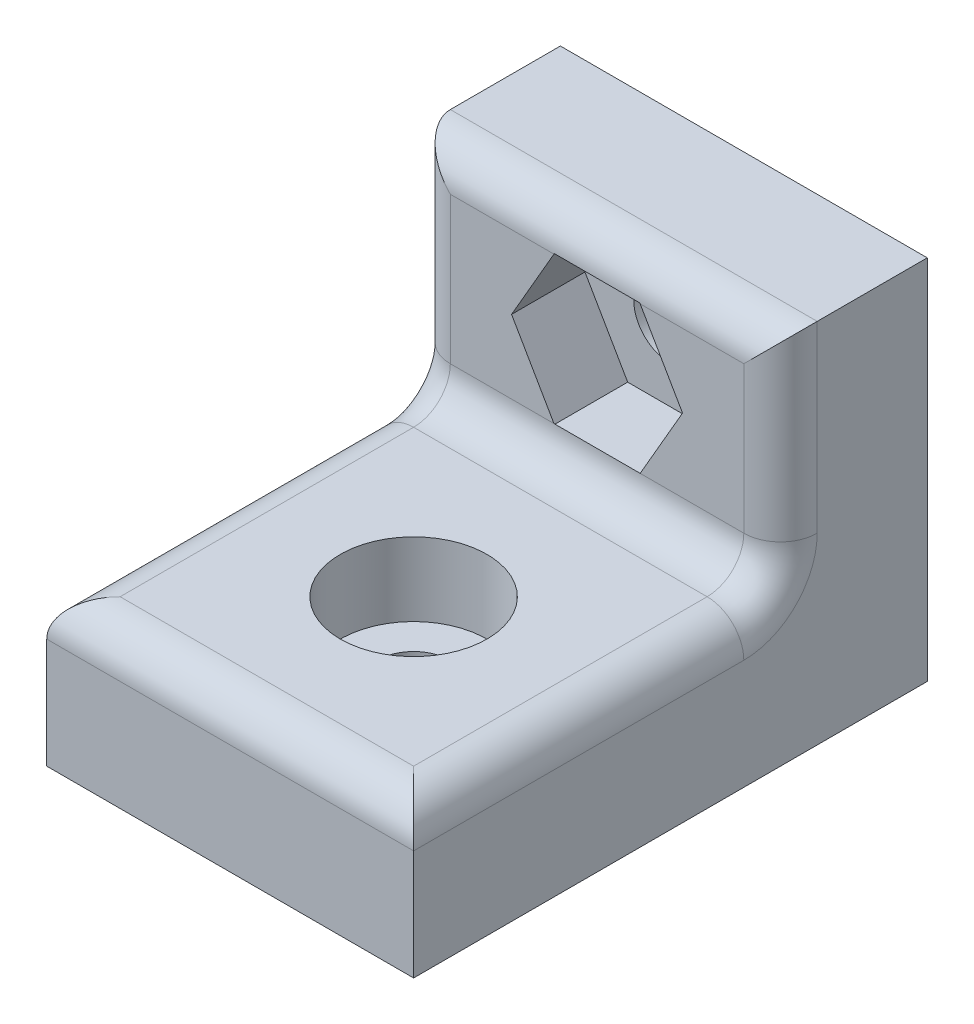
SolidWorks part; units mm, degrees
ref_plane "Plan de face" through (0, 0, 0) normal (0, 0, 1) x (1, 0, 0)
ref_plane "Plan de dessus" through (0, 0, 0) normal (0, 1, 0) x (1, 0, 0)
ref_plane "Plan de droite" through (0, 0, 0) normal (1, 0, 0) x (0, 0, -1)
sketch "Esquisse1" plane through (0, 0, 0) normal (0, 0, 1) x (1, 0, 0)
  line L1 (-5, 10) -> (5, 10)
  line L2 (-5, 10) -> (-5, 0)
  line L3 (-5, 0) -> (5, 0)
  line L4 (5, 10) -> (5, 0)
  dimension "D1" = 10
  dimension "D2" = 10
  dimension "D3" = 5
extrude "Boss.-Extru.1" add sketch "Esquisse1" along normal blind 4
sketch "Esquisse2" plane through (0, 0, 4) normal (0, 0, 1) x (1, 0, 0)
  line L0 (5, 0) -> (5, 10) construction
  line L1 (-5, 0) -> (5, 0)
  line L2 (-5, 0) -> (-5, 4)
  line L3 (-5, 4) -> (5, 4)
  line L4 (5, 0) -> (5, 4)
  dimension "D1" = 4
extrude "Boss.-Extru.2" add sketch "Esquisse2" along normal blind 10
sketch "Esquisse3" plane through (0, 0, 4) normal (0, 0, 1) x (1, 0, 0)
  line L0 (5, 10) -> (-5, 10) construction
  line L1 (-5, 10) -> (-5, 4) construction
  circle A0 centre (0, 7) radius 1
  point P2 (0, 10)
  point P3 (-5, 7)
  dimension "D1" = 2
extrude "Enlèv. mat.-Extru.1" cut sketch "Esquisse3" against normal through all
fillet "Congé1" radius 1 7 edges at (0, 4, 4) (5, 7, 4) (-5, 7, 4) (0, 10, 4) (0, 4, 14) (5, 4, 9) (-5, 4, 9)
sketch "Esquisse4" plane through (0, 4, 0) normal (0, 1, 0) x (1, 0, 0)
  line L0 (5, -14) -> (-5, -14) construction
  line L1 (-5, -14) -> (-5, -4) construction
  circle A0 centre (0, -9) radius 1
  point P0 (0, -14)
  point P1 (-5, -9)
  dimension "D1" = 2
extrude "Enlèv. mat.-Extru.2" cut sketch "Esquisse4" against normal through all
sketch "Esquisse5" plane through (0, 0, 4) normal (0, 0, 1) x (1, 0, 0)
  line L0 (5, 10) -> (-5, 10) construction
  line L1 (1.165, 4.9822) -> (2.33, 7)
  line L2 (2.33, 7) -> (1.165, 9.0178)
  line L3 (1.165, 9.0178) -> (-1.165, 9.0178)
  line L4 (-1.165, 9.0178) -> (-2.33, 7)
  line L5 (-2.33, 7) -> (-1.165, 4.9822)
  line L6 (-1.165, 4.9822) -> (1.165, 4.9822)
  circle A1 centre (0, 7) radius 2.0178 construction
  dimension "D1" = 2.33
extrude "Enlèv. mat.-Extru.3" cut sketch "Esquisse5" against normal blind 2
sketch "Esquisse6" plane through (0, 4, 0) normal (0, 1, 0) x (1, 0, 0)
  circle A0 centre (0, -9) radius 2
  dimension "D1" = 4
extrude "Enlèv. mat.-Extru.4" cut sketch "Esquisse6" against normal blind 2
